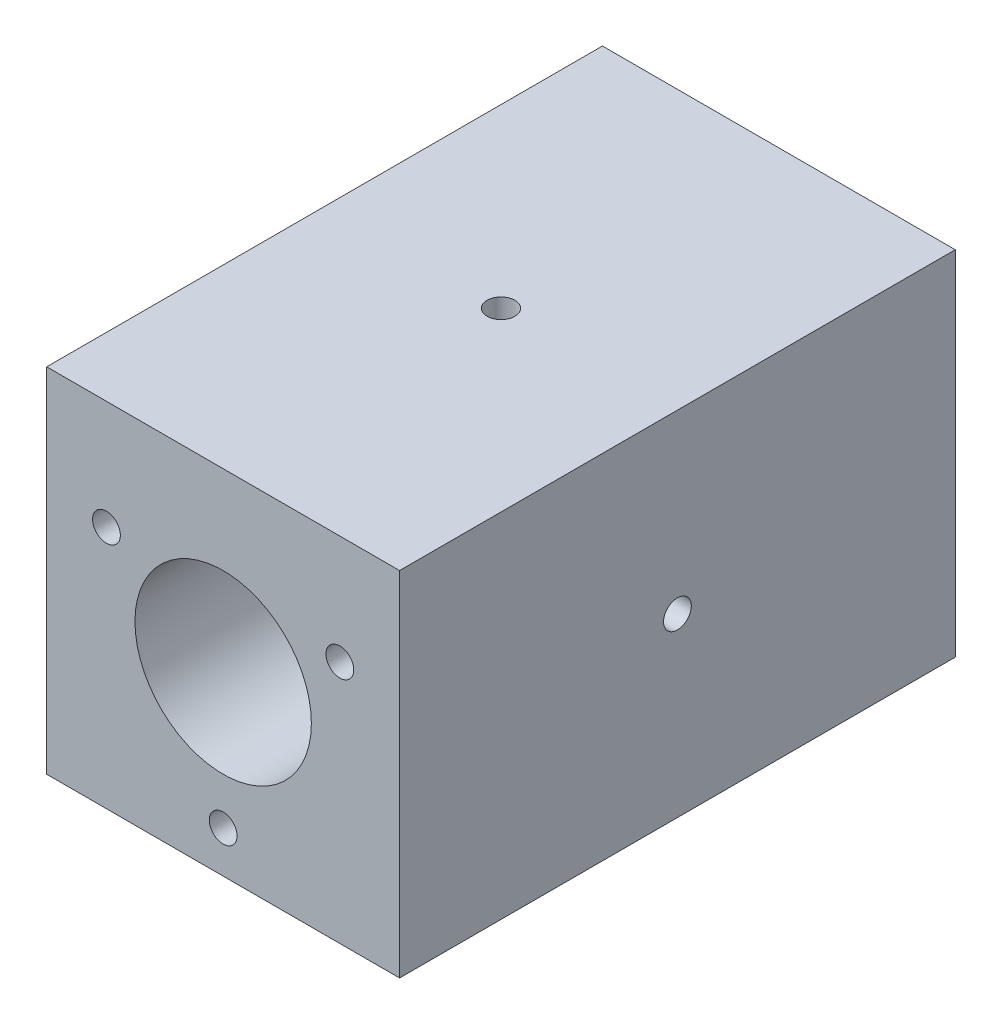
SolidWorks part; units mm, degrees
material "6061-T6 (SS)"
ref_plane "Front Plane" through (0, 0, 0) normal (0, 0, 1) x (1, 0, 0)
ref_plane "Top Plane" through (0, 0, 0) normal (0, 1, 0) x (1, 0, 0)
ref_plane "Right Plane" through (0, 0, 0) normal (1, 0, 0) x (0, 0, -1)
sketch "Sketch1" plane through (0, 0, 0) normal (0, 0, 1) x (1, 0, 0)
  line L1 (15.875, 15.875) -> (-15.875, 15.875)
  line L2 (15.875, 15.875) -> (15.875, -15.875)
  line L3 (15.875, -15.875) -> (-15.875, -15.875)
  line L4 (-15.875, 15.875) -> (-15.875, -15.875)
  line L5 (15.875, 15.875) -> (-15.875, -15.875) construction
  line L6 (15.875, -15.875) -> (-15.875, 15.875) construction
  circle A0 centre (0, 0) radius 7.9375
  circle A1 centre (-10.5, 6.0622) radius 1.25
  circle A2 centre (10.5, 6.0622) radius 1.25
  circle A3 centre (0, -12.1244) radius 1.25
  point P0 (0, 0)
  point P16 (0, 0)
  dimension "D2" = 15.875
  dimension "D3" = 2.5
  dimension "D1" = 31.75
  dimension "D5" = 21
  dimension "D4" = 3
extrude "Boss-Extrude1" add sketch "Sketch1" along normal mid plane 50
sketch "Sketch2" plane through (0, 15.875, 0) normal (0, 1, 0) x (1, 0, 0)
  point P0 (0, 0)
hole_wizard "M3x0.5 Tapped Hole1" positions "Sketch2" profile "Sketch3" tap size "M3x0.5" standard "ANSI Metric"
sketch "Sketch3" plane through (0, 15.875, 0) normal (1, 0, 0) x (0, 0, 1)
  line L0 (0, 0) -> (0, 7.9375)
  line L1 (0, 7.9375) -> (1.25, 7.9375)
  line L2 (1.25, 7.9375) -> (1.25, 0)
  line L5 (1.25, 0) -> (0, 0)
  line L11 (0, -6.35) -> (0, 107.95) construction
  dimension "Thru Tap Drill Dia." = 2.5
  dimension "Thru Tap Drill Depth" = 7.9375
cosmetic thread "Hole Thread1" parameters "D2"=3
sketch "Sketch4" plane through (15.875, 0, 0) normal (1, 0, 0) x (0, 0, -1)
  point P0 (0, 0)
hole_wizard "M3x0.5 Tapped Hole2" positions "Sketch4" profile "Sketch5" tap size "M3x0.5" standard "ANSI Metric"
sketch "Sketch5" plane through (15.875, 0, 0) normal (0, 1, 0) x (0, 0, -1)
  line L0 (0, 0) -> (0, 7.9375)
  line L1 (0, 7.9375) -> (1.25, 7.9375)
  line L2 (1.25, 7.9375) -> (1.25, 0)
  line L5 (1.25, 0) -> (0, 0)
  line L11 (0, -6.35) -> (0, 107.95) construction
  dimension "Thru Tap Drill Dia." = 2.5
  dimension "Thru Tap Drill Depth" = 7.9375
cosmetic thread "Hole Thread2" parameters "D2"=3
